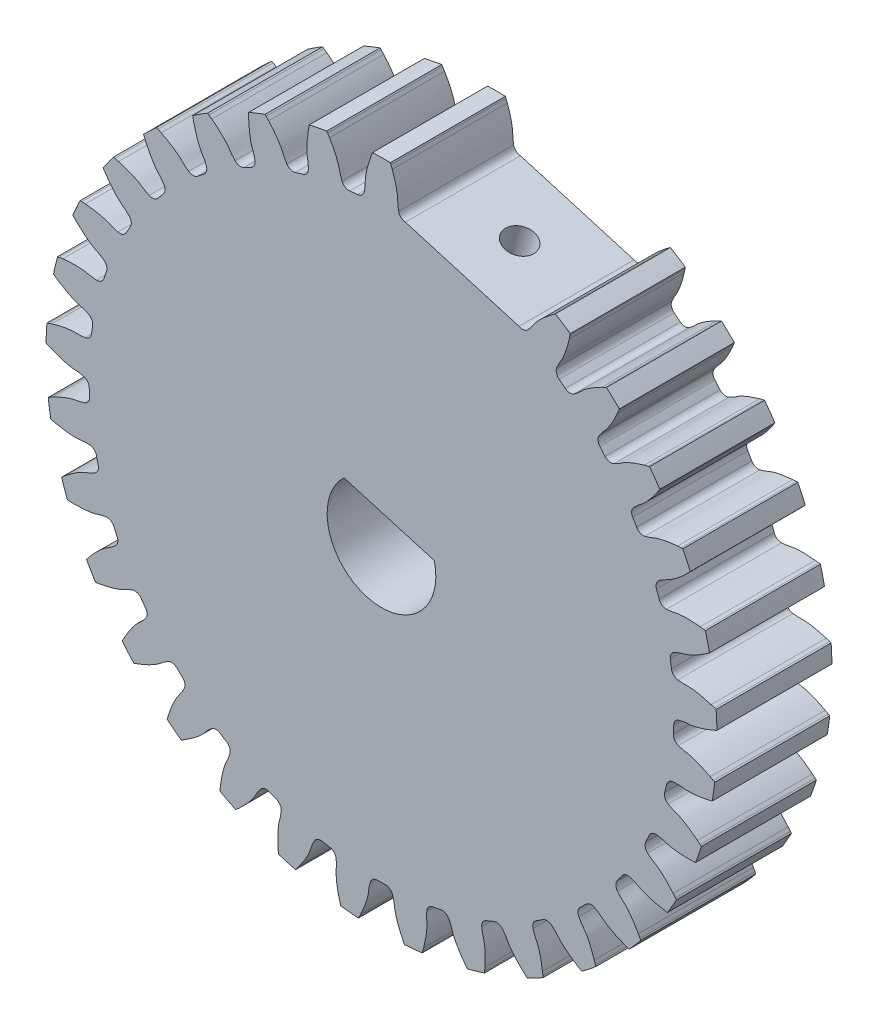
SolidWorks part; units mm, degrees
ref_plane "Front Plane" through (0, 0, 0) normal (0, 0, 1) x (1, 0, 0)
ref_plane "Top Plane" through (0, 0, 0) normal (0, 1, 0) x (1, 0, 0)
ref_plane "Right Plane" through (0, 0, 0) normal (1, 0, 0) x (0, 0, -1)
sketch "Sketch1" plane through (0, 0, 0) normal (0, 0, 1) x (1, 0, 0)
  line L0 (1.3177, 16.0878) -> (7.5892, 14.2464)
  line L1 (-2.0702, 2.1712) -> (2.9154, 0.7073)
  arc A0 (-2.0702, 2.1712) -> (2.9154, 0.7073) centre (0, 0) ccw
  arc A2 (0.9461, 16.421) -> (1.3177, 16.0878) centre (1.3514, 16.4992) ccw
  arc A4 (7.5892, 14.2464) -> (8.0819, 14.3257) centre (7.7833, 14.6106) ccw
  arc A5 (9.6738, 13.3027) -> (9.8063, 12.8215) centre (10.057, 13.1494) ccw
  arc A6 (10.1482, 12.5526) -> (9.8063, 12.8215) centre (0, 0) ccw
  arc A7 (10.1482, 12.5526) -> (10.647, 12.5373) centre (10.4077, 12.8736) ccw
  arc A8 (12.0165, 11.2315) -> (12.0556, 10.734) centre (12.3638, 11.0084) ccw
  arc A9 (12.3404, 10.4052) -> (12.0556, 10.734) centre (0, 0) ccw
  arc A10 (12.3404, 10.4052) -> (12.8273, 10.2958) centre (12.6559, 10.6713) ccw
  arc A11 (13.925, 8.7544) -> (13.8691, 8.2585) centre (14.2237, 8.4696) ccw
  arc A12 (14.0866, 7.8818) -> (13.8691, 8.2585) centre (0, 0) ccw
  arc A13 (14.0866, 7.8818) -> (14.544, 7.6822) centre (14.4468, 8.0833) ccw
  arc A14 (15.3301, 5.9609) -> (15.1814, 5.4845) centre (15.5696, 5.6247) ccw
  arc A15 (15.3237, 5.0734) -> (15.1814, 5.4845) centre (0, 0) ccw
  arc A16 (15.3237, 5.0734) -> (15.735, 4.7909) centre (15.7155, 5.2032) ccw
  arc A17 (16.1812, 2.9519) -> (15.945, 2.5123) centre (16.3527, 2.5765) ccw
  arc A18 (16.0069, 2.0817) -> (15.945, 2.5123) centre (0, 0) ccw
  arc A19 (16.0069, 2.0817) -> (16.3574, 1.7264) centre (16.4162, 2.135) ccw
  arc A20 (16.4474, -0.1637) -> (16.1323, -0.5507) centre (16.5448, -0.5648) ccw
  arc A21 (16.1116, -0.9852) -> (16.1323, -0.5507) centre (0, 0) ccw
  arc A22 (16.1116, -0.9852) -> (16.3885, -1.4004) centre (16.5236, -1.0104) ccw
  arc A23 (16.1192, -3.2735) -> (15.7365, -3.5938) centre (16.1389, -3.6857) ccw
  arc A24 (15.634, -4.0166) -> (15.7365, -3.5938) centre (0, 0) ccw
  arc A25 (15.634, -4.0166) -> (15.8273, -4.4767) centre (16.0338, -4.1193) ccw
  arc A26 (15.2084, -6.2649) -> (14.772, -6.5071) centre (15.1497, -6.6734) ccw
  arc A27 (14.5913, -6.9027) -> (14.772, -6.5071) centre (0, 0) ccw
  arc A28 (14.5913, -6.9027) -> (14.6941, -7.3911) centre (14.9644, -7.0792) ccw
  arc A29 (13.7479, -9.0299) -> (13.2736, -9.1851) centre (13.613, -9.42) ccw
  arc A30 (13.0213, -9.5394) -> (13.2736, -9.1851) centre (0, 0) ccw
  arc A31 (13.0213, -9.5394) -> (13.0297, -10.0384) centre (13.3543, -9.7833) ccw
  arc A32 (11.7906, -11.4685) -> (11.2954, -11.5312) centre (11.5843, -11.826) ccw
  arc A33 (10.9806, -11.8313) -> (11.2954, -11.5312) centre (0, 0) ccw
  arc A34 (10.9806, -11.8313) -> (10.8945, -12.3229) centre (11.2614, -12.1339) ccw
  arc A35 (9.4071, -13.4926) -> (8.909, -13.4604) centre (9.1368, -13.8046) ccw
  arc A36 (8.5431, -13.6956) -> (8.909, -13.4604) centre (0, 0) ccw
  arc A37 (8.5431, -13.6956) -> (8.3655, -14.162) centre (8.7616, -14.0458) ccw
  arc A38 (6.6836, -15.0291) -> (6.2006, -14.9032) centre (6.3592, -15.2843) ccw
  arc A39 (5.7968, -15.0649) -> (6.2006, -14.9032) centre (0, 0) ccw
  arc A40 (5.7968, -15.0649) -> (5.5341, -15.4893) centre (5.945, -15.4501) ccw
  arc A41 (3.7185, -16.0224) -> (3.2681, -15.8074) centre (3.3517, -16.2116) ccw
  arc A42 (2.841, -15.8897) -> (3.2681, -15.8074) centre (0, 0) ccw
  arc A43 (2.841, -15.8897) -> (2.5028, -16.2567) centre (2.9136, -16.296) ccw
  arc A44 (0.6191, -16.4366) -> (0.2175, -16.1402) centre (0.2231, -16.5529) ccw
  arc A45 (-0.2175, -16.1402) -> (0.2175, -16.1402) centre (0, 0) ccw
  arc A46 (-0.2175, -16.1402) -> (-0.6191, -16.4366) centre (-0.2231, -16.5529) ccw
  arc A47 (-2.5028, -16.2567) -> (-2.841, -15.8897) centre (-2.9136, -16.296) ccw
  arc A48 (-3.2681, -15.8074) -> (-2.841, -15.8897) centre (0, 0) ccw
  arc A49 (-3.2681, -15.8074) -> (-3.7185, -16.0224) centre (-3.3517, -16.2116) ccw
  arc A50 (-5.5341, -15.4893) -> (-5.7968, -15.0649) centre (-5.945, -15.4501) ccw
  arc A51 (-6.2006, -14.9032) -> (-5.7968, -15.0649) centre (0, 0) ccw
  arc A52 (-6.2006, -14.9032) -> (-6.6836, -15.0291) centre (-6.3592, -15.2843) ccw
  arc A53 (-8.3655, -14.162) -> (-8.5431, -13.6956) centre (-8.7616, -14.0458) ccw
  arc A54 (-8.909, -13.4604) -> (-8.5431, -13.6956) centre (0, 0) ccw
  arc A55 (-8.909, -13.4604) -> (-9.4071, -13.4926) centre (-9.1368, -13.8046) ccw
  arc A56 (-10.8945, -12.3229) -> (-10.9806, -11.8313) centre (-11.2614, -12.1339) ccw
  arc A57 (-11.2954, -11.5312) -> (-10.9806, -11.8313) centre (0, 0) ccw
  arc A58 (-11.2954, -11.5312) -> (-11.7906, -11.4685) centre (-11.5843, -11.826) ccw
  arc A59 (-13.0297, -10.0384) -> (-13.0213, -9.5394) centre (-13.3543, -9.7833) ccw
  arc A60 (-13.2736, -9.1851) -> (-13.0213, -9.5394) centre (0, 0) ccw
  arc A61 (-13.2736, -9.1851) -> (-13.7479, -9.0299) centre (-13.613, -9.42) ccw
  arc A62 (-14.6941, -7.3911) -> (-14.5913, -6.9027) centre (-14.9644, -7.0792) ccw
  arc A63 (-14.772, -6.5071) -> (-14.5913, -6.9027) centre (0, 0) ccw
  arc A64 (-14.772, -6.5071) -> (-15.2084, -6.2649) centre (-15.1497, -6.6734) ccw
  arc A65 (-15.8273, -4.4767) -> (-15.634, -4.0166) centre (-16.0338, -4.1193) ccw
  arc A66 (-15.7365, -3.5938) -> (-15.634, -4.0166) centre (0, 0) ccw
  arc A67 (-15.7365, -3.5938) -> (-16.1192, -3.2735) centre (-16.1389, -3.6857) ccw
  arc A68 (-16.3885, -1.4004) -> (-16.1116, -0.9852) centre (-16.5236, -1.0104) ccw
  arc A69 (-16.1323, -0.5507) -> (-16.1116, -0.9852) centre (0, 0) ccw
  arc A70 (-16.1323, -0.5507) -> (-16.4474, -0.1637) centre (-16.5448, -0.5648) ccw
  arc A71 (-16.3574, 1.7264) -> (-16.0069, 2.0817) centre (-16.4162, 2.135) ccw
  arc A72 (-15.945, 2.5123) -> (-16.0069, 2.0817) centre (0, 0) ccw
  arc A73 (-15.945, 2.5123) -> (-16.1812, 2.9519) centre (-16.3527, 2.5765) ccw
  arc A74 (-15.735, 4.7909) -> (-15.3237, 5.0734) centre (-15.7155, 5.2032) ccw
  arc A75 (-15.1814, 5.4845) -> (-15.3237, 5.0734) centre (0, 0) ccw
  arc A76 (-15.1814, 5.4845) -> (-15.3301, 5.9609) centre (-15.5696, 5.6247) ccw
  arc A77 (-14.544, 7.6822) -> (-14.0866, 7.8818) centre (-14.4468, 8.0833) ccw
  arc A78 (-13.8691, 8.2585) -> (-14.0866, 7.8818) centre (0, 0) ccw
  arc A79 (-13.8691, 8.2585) -> (-13.925, 8.7544) centre (-14.2237, 8.4696) ccw
  arc A80 (-12.8273, 10.2958) -> (-12.3404, 10.4052) centre (-12.6559, 10.6713) ccw
  arc A81 (-12.0556, 10.734) -> (-12.3404, 10.4052) centre (0, 0) ccw
  arc A82 (-12.0556, 10.734) -> (-12.0165, 11.2315) centre (-12.3638, 11.0084) ccw
  arc A83 (-10.647, 12.5373) -> (-10.1482, 12.5526) centre (-10.4077, 12.8736) ccw
  arc A84 (-9.8063, 12.8215) -> (-10.1482, 12.5526) centre (0, 0) ccw
  arc A85 (-9.8063, 12.8215) -> (-9.6738, 13.3027) centre (-10.057, 13.1494) ccw
  arc A86 (-8.0819, 14.3257) -> (-7.5892, 14.2464) centre (-7.7833, 14.6106) ccw
  arc A87 (-7.2026, 14.4457) -> (-7.5892, 14.2464) centre (0, 0) ccw
  arc A88 (-7.2026, 14.4457) -> (-6.9814, 14.8931) centre (-7.3867, 14.8151) ccw
  arc A89 (-5.2247, 15.5964) -> (-4.7559, 15.4252) centre (-4.8775, 15.8196) ccw
  arc A90 (-4.3386, 15.5477) -> (-4.7559, 15.4252) centre (0, 0) ccw
  arc A91 (-4.3386, 15.5477) -> (-4.0367, 15.9452) centre (-4.4495, 15.9453) ccw
  arc A92 (-2.1786, 16.3033) -> (-1.7507, 16.0465) centre (-1.7955, 16.4568) ccw
  arc A93 (-1.3177, 16.0878) -> (-1.7507, 16.0465) centre (0, 0) ccw
  arc A94 (-1.3177, 16.0878) -> (-0.9461, 16.421) centre (-1.3514, 16.4992) ccw
  arc A95 (10.4216, 15.3105) -> (9.5977, 15.84) centre (0, 0) ccw
  arc A96 (-14.3129, -11.7542) -> (-13.6715, -12.4944) centre (0, 0) ccw
  arc A97 (-16.6378, 8.1366) -> (-17.0447, 7.2457) centre (0, 0) ccw
  arc A98 (17.0447, 7.2457) -> (16.6378, 8.1366) centre (0, 0) ccw
  arc A99 (11.0599, -14.856) -> (11.8297, -14.2506) centre (0, 0) ccw
  arc A100 (-18.3956, -2.1502) -> (-18.2562, -3.1196) centre (0, 0) ccw
  arc A101 (17.3359, -6.5182) -> (17.6562, -5.5927) centre (0, 0) ccw
  arc A102 (4.7462, -17.9024) -> (5.6859, -17.6264) centre (0, 0) ccw
  arc A103 (18.1079, 3.889) -> (17.877, 4.8408) centre (0, 0) ccw
  arc A104 (-12.422, 13.7374) -> (-13.1308, 13.0615) centre (0, 0) ccw
  arc A105 (-17.877, 4.8408) -> (-18.1079, 3.889) centre (0, 0) ccw
  arc A106 (-9.5977, 15.84) -> (-10.4216, 15.3105) centre (0, 0) ccw
  arc A107 (-5.6859, -17.6264) -> (-4.7462, -17.9024) centre (0, 0) ccw
  arc A108 (0.4897, 18.5144) -> (-0.4897, 18.5144) centre (0, 0) ccw
  arc A109 (-11.8297, -14.2506) -> (-11.0599, -14.856) centre (0, 0) ccw
  arc A110 (-16.2787, -8.8331) -> (-15.7891, -9.6813) centre (0, 0) ccw
  arc A111 (1.2724, -18.4771) -> (2.2474, -18.384) centre (0, 0) ccw
  arc A112 (-3.023, 18.2725) -> (-3.9847, 18.0871) centre (0, 0) ccw
  arc A113 (18.5167, 0.3918) -> (18.4701, 1.3701) centre (0, 0) ccw
  arc A114 (13.1308, 13.0615) -> (12.422, 13.7374) centre (0, 0) ccw
  arc A115 (8.0485, -16.6806) -> (8.919, -16.2318) centre (0, 0) ccw
  arc A116 (13.6715, -12.4944) -> (14.3129, -11.7542) centre (0, 0) ccw
  arc A117 (-18.4701, 1.3701) -> (-18.5167, 0.3918) centre (0, 0) ccw
  arc A118 (-2.2474, -18.384) -> (-1.2724, -18.4771) centre (0, 0) ccw
  arc A119 (15.3654, 10.3405) -> (14.7973, 11.1383) centre (0, 0) ccw
  arc A120 (-8.919, -16.2318) -> (-8.0485, -16.6806) centre (0, 0) ccw
  arc A121 (15.7891, -9.6813) -> (16.2787, -8.8331) centre (0, 0) ccw
  arc A122 (-14.7973, 11.1383) -> (-15.3654, 10.3405) centre (0, 0) ccw
  arc A123 (-17.6562, -5.5927) -> (-17.3359, -6.5182) centre (0, 0) ccw
  arc A124 (18.2562, -3.1196) -> (18.3956, -2.1502) centre (0, 0) ccw
  arc A125 (-6.4265, 17.3701) -> (-7.3357, 17.0061) centre (0, 0) ccw
  spline S31 degree 3 poles (-11.7906, -11.4685) (-11.8581, -11.5075) (-11.9247, -11.5479) (-12.0526, -11.6363) (-12.1128, -11.6859) (-12.2326, -11.7859) (-12.2929, -11.8353) (-12.421, -11.9234) (-12.4877, -11.9637) (-12.8258, -12.1584) (-13.1079, -12.2893) (-13.4001, -12.3987) knots 0 0 0 0 0.125 0.125 0.25 0.25 0.375 0.375 0.5 0.5 1 1 1 1
  spline S32 degree 3 poles (-6.6836, -15.0291) (-6.7318, -15.0904) (-6.7786, -15.1527) (-6.8644, -15.2823) (-6.9019, -15.3507) (-6.9759, -15.4881) (-7.0136, -15.5563) (-7.0998, -15.6857) (-7.1467, -15.7479) (-7.3882, -16.0543) (-7.6014, -16.2807) (-7.8321, -16.4909) knots 0 0 0 0 0.125 0.125 0.25 0.25 0.375 0.375 0.5 0.5 1 1 1 1
  spline S33 degree 3 poles (-3.7185, -16.0224) (-3.7543, -16.0917) (-3.7885, -16.1617) (-3.8482, -16.3052) (-3.872, -16.3795) (-3.9187, -16.5284) (-3.9428, -16.6025) (-4.0029, -16.7459) (-4.0372, -16.8158) (-4.2164, -17.1624) (-4.3829, -17.4251) (-4.5696, -17.6751) knots 0 0 0 0 0.125 0.125 0.25 0.25 0.375 0.375 0.5 0.5 1 1 1 1
  spline S34 degree 3 poles (-16.1812, 2.9519) (-16.2521, 2.9843) (-16.3237, 3.0152) (-16.4699, 3.068) (-16.5452, 3.0883) (-16.6961, 3.1278) (-16.7713, 3.1484) (-16.9174, 3.2016) (-16.9889, 3.2325) (-17.3436, 3.395) (-17.6139, 3.5488) (-17.8725, 3.7234) knots 0 0 0 0 0.125 0.125 0.25 0.25 0.375 0.375 0.5 0.5 1 1 1 1
  spline S35 degree 3 poles (-4.0367, 15.9452) (-4.0367, 16.0232) (-4.0384, 16.1011) (-4.0511, 16.256) (-4.0639, 16.3329) (-4.0906, 16.4867) (-4.1032, 16.5636) (-4.1155, 16.7186) (-4.117, 16.7965) (-4.1166, 17.1866) (-4.0889, 17.4964) (-4.0376, 17.8042) knots 0 0 0 0 0.125 0.125 0.25 0.25 0.375 0.375 0.5 0.5 1 1 1 1
  spline S36 degree 3 poles (-16.1192, -3.2735) (-16.1971, -3.2697) (-16.275, -3.2677) (-16.4304, -3.273) (-16.5078, -3.2821) (-16.6626, -3.3015) (-16.7401, -3.3104) (-16.8955, -3.3153) (-16.9733, -3.3132) (-17.363, -3.2941) (-17.6712, -3.2518) (-17.9761, -3.1858) knots 0 0 0 0 0.125 0.125 0.25 0.25 0.375 0.375 0.5 0.5 1 1 1 1
  spline S37 degree 3 poles (-16.4474, -0.1637) (-16.5232, -0.1453) (-16.5993, -0.1286) (-16.7529, -0.1044) (-16.8306, -0.0987) (-16.9863, -0.0884) (-17.0641, -0.0825) (-17.2176, -0.0579) (-17.2936, -0.0411) (-17.6727, 0.0514) (-17.9672, 0.1513) (-18.2542, 0.2737) knots 0 0 0 0 0.125 0.125 0.25 0.25 0.375 0.375 0.5 0.5 1 1 1 1
  spline S38 degree 3 poles (-15.3301, 5.9609) (-15.3936, 6.0062) (-15.4581, 6.0499) (-15.5916, 6.1295) (-15.6617, 6.1637) (-15.8024, 6.2311) (-15.8724, 6.2655) (-16.0058, 6.3454) (-16.0701, 6.3893) (-16.3876, 6.616) (-16.624, 6.8182) (-16.8449, 7.0385) knots 0 0 0 0 0.125 0.125 0.25 0.25 0.375 0.375 0.5 0.5 1 1 1 1
  spline S39 degree 3 poles (5.5341, -15.4893) (5.5415, -15.5669) (5.5506, -15.6443) (5.578, -15.7973) (5.598, -15.8727) (5.6393, -16.0232) (5.6591, -16.0986) (5.686, -16.2517) (5.695, -16.3291) (5.7316, -16.7175) (5.7336, -17.0285) (5.7117, -17.3398) knots 0 0 0 0 0.125 0.125 0.25 0.25 0.375 0.375 0.5 0.5 1 1 1 1
  spline S40 degree 3 poles (14.6941, -7.3911) (14.753, -7.4422) (14.813, -7.4919) (14.9384, -7.5838) (15.0049, -7.6245) (15.1386, -7.705) (15.205, -7.7459) (15.3301, -7.8381) (15.39, -7.8879) (15.6846, -8.1438) (15.9006, -8.3675) (16.0995, -8.6079) knots 0 0 0 0 0.125 0.125 0.25 0.25 0.375 0.375 0.5 0.5 1 1 1 1
  spline S41 degree 3 poles (2.5028, -16.2567) (2.4953, -16.3344) (2.4896, -16.412) (2.4875, -16.5675) (2.493, -16.6453) (2.505, -16.8009) (2.5102, -16.8786) (2.5076, -17.0341) (2.5018, -17.1118) (2.4642, -17.5001) (2.4073, -17.8059) (2.3269, -18.1074) knots 0 0 0 0 0.125 0.125 0.25 0.25 0.375 0.375 0.5 0.5 1 1 1 1
  spline S42 degree 3 poles (12.8273, 10.2958) (12.8983, 10.3282) (12.9684, 10.3621) (13.1041, 10.438) (13.1688, 10.4816) (13.2975, 10.5698) (13.3623, 10.6132) (13.4981, 10.6887) (13.5683, 10.7225) (13.9234, 10.8841) (14.2167, 10.9877) (14.518, 11.0688) knots 0 0 0 0 0.125 0.125 0.25 0.25 0.375 0.375 0.5 0.5 1 1 1 1
  spline S43 degree 3 poles (8.3655, -14.162) (8.3875, -14.2369) (8.411, -14.3111) (8.4668, -14.4562) (8.5008, -14.5264) (8.5698, -14.6664) (8.6035, -14.7367) (8.6589, -14.8819) (8.6824, -14.9562) (8.7918, -15.3307) (8.8526, -15.6357) (8.89, -15.9455) knots 0 0 0 0 0.125 0.125 0.25 0.25 0.375 0.375 0.5 0.5 1 1 1 1
  spline S44 degree 3 poles (-13.925, 8.7544) (-13.9788, 8.8109) (-14.0338, 8.8661) (-14.1498, 8.9695) (-14.2122, 9.0163) (-14.3376, 9.1091) (-14.3998, 9.1561) (-14.5157, 9.2598) (-14.5705, 9.3151) (-14.8394, 9.5978) (-15.0332, 9.8411) (-15.2084, 10.0992) knots 0 0 0 0 0.125 0.125 0.25 0.25 0.375 0.375 0.5 0.5 1 1 1 1
  spline S45 degree 3 poles (10.647, 12.5373) (10.7106, 12.5826) (10.773, 12.6291) (10.8919, 12.7293) (10.9471, 12.7844) (11.0568, 12.8953) (11.1122, 12.9502) (11.2314, 13.0501) (11.2939, 13.0966) (11.612, 13.3225) (11.8803, 13.4797) (12.1608, 13.6163) knots 0 0 0 0 0.125 0.125 0.25 0.25 0.375 0.375 0.5 0.5 1 1 1 1
  spline S46 degree 3 poles (-0.6191, -16.4366) (-0.6411, -16.5114) (-0.6614, -16.5866) (-0.6929, -16.7389) (-0.7022, -16.8163) (-0.7199, -16.9713) (-0.7295, -17.0487) (-0.7614, -17.2008) (-0.7818, -17.276) (-0.8922, -17.6502) (-1.006, -17.9397) (-1.142, -18.2205) knots 0 0 0 0 0.125 0.125 0.25 0.25 0.375 0.375 0.5 0.5 1 1 1 1
  spline S47 degree 3 poles (15.735, 4.7909) (15.813, 4.7946) (15.8907, 4.8) (16.0449, 4.82) (16.1211, 4.8365) (16.2734, 4.8705) (16.3496, 4.8867) (16.5038, 4.9063) (16.5816, 4.9116) (16.9713, 4.9297) (17.282, 4.9168) (17.5919, 4.8802) knots 0 0 0 0 0.125 0.125 0.25 0.25 0.375 0.375 0.5 0.5 1 1 1 1
  spline S48 degree 3 poles (-6.9814, 14.8931) (-6.9962, 14.9697) (-7.0126, 15.0458) (-7.0543, 15.1956) (-7.0815, 15.2687) (-7.1368, 15.4146) (-7.1637, 15.4877) (-7.2051, 15.6376) (-7.2214, 15.7138) (-7.2948, 16.097) (-7.3263, 16.4064) (-7.3341, 16.7183) knots 0 0 0 0 0.125 0.125 0.25 0.25 0.375 0.375 0.5 0.5 1 1 1 1
  spline S49 degree 3 poles (-13.7479, -9.0299) (-13.8217, -9.0554) (-13.8947, -9.0825) (-14.037, -9.1451) (-14.1055, -9.1824) (-14.242, -9.2579) (-14.3106, -9.295) (-14.453, -9.3572) (-14.5261, -9.3842) (-14.895, -9.5113) (-15.1968, -9.5866) (-15.5044, -9.6387) knots 0 0 0 0 0.125 0.125 0.25 0.25 0.375 0.375 0.5 0.5 1 1 1 1
  spline S50 degree 3 poles (16.3885, -1.4004) (16.4622, -1.426) (16.5364, -1.4498) (16.6869, -1.4886) (16.7638, -1.5016) (16.9178, -1.5266) (16.9947, -1.5399) (17.1451, -1.579) (17.2192, -1.603) (17.5878, -1.731) (17.8715, -1.8585) (18.1455, -2.0077) knots 0 0 0 0 0.125 0.125 0.25 0.25 0.375 0.375 0.5 0.5 1 1 1 1
  spline S51 degree 3 poles (14.544, 7.6822) (14.6198, 7.7005) (14.6951, 7.7206) (14.8427, 7.7694) (14.9144, 7.8) (15.0575, 7.8622) (15.1293, 7.8926) (15.2771, 7.941) (15.3524, 7.9609) (15.7316, 8.0524) (16.0392, 8.0986) (16.3504, 8.1213) knots 0 0 0 0 0.125 0.125 0.25 0.25 0.375 0.375 0.5 0.5 1 1 1 1
  spline S52 degree 3 poles (16.3574, 1.7264) (16.4346, 1.7153) (16.5119, 1.7059) (16.6671, 1.6964) (16.745, 1.6981) (16.901, 1.7027) (16.979, 1.7042) (17.1341, 1.6943) (17.2114, 1.6847) (17.5975, 1.6288) (17.9002, 1.5573) (18.1976, 1.4627) knots 0 0 0 0 0.125 0.125 0.25 0.25 0.375 0.375 0.5 0.5 1 1 1 1
  spline S53 degree 3 poles (-9.4071, -13.4926) (-9.466, -13.5437) (-9.5238, -13.596) (-9.6326, -13.707) (-9.6823, -13.7671) (-9.781, -13.888) (-9.8309, -13.9479) (-9.94, -14.0586) (-9.9978, -14.1108) (-10.293, -14.3659) (-10.5452, -14.5479) (-10.8114, -14.7107) knots 0 0 0 0 0.125 0.125 0.25 0.25 0.375 0.375 0.5 0.5 1 1 1 1
  spline S54 degree 3 poles (-9.6738, 13.3027) (-9.7028, 13.3751) (-9.7333, 13.4468) (-9.8026, 13.5859) (-9.8431, 13.6526) (-9.9251, 13.7854) (-9.9654, 13.8521) (-10.0343, 13.9914) (-10.0647, 14.0632) (-10.2093, 14.4255) (-10.2988, 14.7234) (-10.3655, 15.0282) knots 0 0 0 0 0.125 0.125 0.25 0.25 0.375 0.375 0.5 0.5 1 1 1 1
  spline S55 degree 3 poles (13.0297, -10.0384) (13.078, -10.0998) (13.1274, -10.1599) (13.2332, -10.2739) (13.2908, -10.3264) (13.4068, -10.4307) (13.4643, -10.4834) (13.5697, -10.5977) (13.6191, -10.6579) (13.8599, -10.9649) (14.0297, -11.2255) (14.1796, -11.4992) knots 0 0 0 0 0.125 0.125 0.25 0.25 0.375 0.375 0.5 0.5 1 1 1 1
  spline S56 degree 3 poles (-12.0165, 11.2315) (-12.0587, 11.2972) (-12.1022, 11.3618) (-12.1967, 11.4853) (-12.249, 11.543) (-12.3546, 11.6579) (-12.4068, 11.7158) (-12.5009, 11.8396) (-12.5443, 11.9043) (-12.7549, 12.2327) (-12.8991, 12.5083) (-13.0223, 12.7949) knots 0 0 0 0 0.125 0.125 0.25 0.25 0.375 0.375 0.5 0.5 1 1 1 1
  spline S57 degree 3 poles (-15.2084, -6.2649) (-15.2856, -6.276) (-15.3625, -6.2887) (-15.514, -6.3233) (-15.5883, -6.347) (-15.7367, -6.3953) (-15.8111, -6.4187) (-15.9627, -6.4529) (-16.0396, -6.4655) (-16.4258, -6.5206) (-16.7364, -6.5373) (-17.0483, -6.5303) knots 0 0 0 0 0.125 0.125 0.25 0.25 0.375 0.375 0.5 0.5 1 1 1 1
  spline S58 degree 3 poles (15.8273, -4.4767) (15.8949, -4.5157) (15.9631, -4.5532) (16.1037, -4.6197) (16.1767, -4.647) (16.3232, -4.7007) (16.3961, -4.7283) (16.5365, -4.7952) (16.6047, -4.8328) (16.9423, -5.0283) (17.1968, -5.2071) (17.4377, -5.4054) knots 0 0 0 0 0.125 0.125 0.25 0.25 0.375 0.375 0.5 0.5 1 1 1 1
  spline S59 degree 3 poles (10.8945, -12.3229) (10.9302, -12.3923) (10.9674, -12.4607) (11.0497, -12.5926) (11.0963, -12.6551) (11.1905, -12.7795) (11.237, -12.8421) (11.3189, -12.9743) (11.356, -13.0428) (11.5343, -13.3898) (11.6517, -13.6778) (11.7471, -13.9749) knots 0 0 0 0 0.125 0.125 0.25 0.25 0.375 0.375 0.5 0.5 1 1 1 1
  spline S60 degree 3 poles (8.0819, 14.3257) (8.1358, 14.3822) (8.1883, 14.4397) (8.286, 14.5606) (8.3298, 14.6251) (8.4166, 14.7548) (8.4606, 14.8192) (8.5586, 14.9398) (8.6113, 14.9973) (8.8808, 15.2793) (9.1146, 15.4844) (9.3642, 15.6717) knots 0 0 0 0 0.125 0.125 0.25 0.25 0.375 0.375 0.5 0.5 1 1 1 1
  spline S61 degree 3 poles (-6.229, 17.1607) (-6.0194, 16.9296) (-5.8286, 16.6837) (-5.6173, 16.3559) (-5.5766, 16.2895) (-5.5031, 16.1525) (-5.4721, 16.081) (-5.4115, 15.9372) (-5.3807, 15.8656) (-5.3076, 15.7284) (-5.2669, 15.662) (-5.2247, 15.5964) knots 0 0 0 0 0.5 0.5 0.625 0.625 0.75 0.75 0.875 0.875 1 1 1 1
  spline S62 degree 3 poles (-9.3642, 15.6717) (-9.1146, 15.4844) (-8.8807, 15.2792) (-8.6112, 14.9972) (-8.5586, 14.9398) (-8.4605, 14.8191) (-8.4165, 14.7548) (-8.3298, 14.6251) (-8.286, 14.5606) (-8.1883, 14.4397) (-8.1358, 14.3822) (-8.0819, 14.3257) knots 0 0 0 0 0.5 0.5 0.625 0.625 0.75 0.75 0.875 0.875 1 1 1 1
  spline S63 degree 3 poles (-11.7471, -13.9749) (-11.6517, -13.6778) (-11.5342, -13.3896) (-11.3559, -13.0427) (-11.3188, -12.9742) (-11.2369, -12.8421) (-11.1905, -12.7795) (-11.0963, -12.6551) (-11.0497, -12.5926) (-10.9674, -12.4607) (-10.9302, -12.3922) (-10.8945, -12.3229) knots 0 0 0 0 0.5 0.5 0.625 0.625 0.75 0.75 0.875 0.875 1 1 1 1
  spline S64 degree 3 poles (-8.89, -15.9455) (-8.8526, -15.6357) (-8.7918, -15.3305) (-8.6824, -14.9561) (-8.6589, -14.8818) (-8.6035, -14.7366) (-8.5697, -14.6663) (-8.5008, -14.5264) (-8.4668, -14.4562) (-8.411, -14.3111) (-8.3875, -14.2369) (-8.3655, -14.162) knots 0 0 0 0 0.5 0.5 0.625 0.625 0.75 0.75 0.875 0.875 1 1 1 1
  spline S65 degree 3 poles (-16.0995, -8.6079) (-15.9006, -8.3675) (-15.6844, -8.1436) (-15.39, -7.8878) (-15.3301, -7.838) (-15.2049, -7.7458) (-15.1385, -7.705) (-15.0049, -7.6245) (-14.9383, -7.5838) (-14.813, -7.4919) (-14.753, -7.4422) (-14.6941, -7.3911) knots 0 0 0 0 0.5 0.5 0.625 0.625 0.75 0.75 0.875 0.875 1 1 1 1
  spline S66 degree 3 poles (16.8449, 7.0385) (16.624, 6.8182) (16.3875, 6.6159) (16.0701, 6.3892) (16.0057, 6.3453) (15.8724, 6.2654) (15.8024, 6.2311) (15.6617, 6.1637) (15.5916, 6.1295) (15.458, 6.0499) (15.3936, 6.0061) (15.3301, 5.9609) knots 0 0 0 0 0.5 0.5 0.625 0.625 0.75 0.75 0.875 0.875 1 1 1 1
  spline S67 degree 3 poles (-14.518, 11.0688) (-14.2167, 10.9877) (-13.9233, 10.8841) (-13.5683, 10.7225) (-13.4981, 10.6887) (-13.3622, 10.6132) (-13.2975, 10.5698) (-13.1687, 10.4816) (-13.1041, 10.438) (-12.9684, 10.3621) (-12.8983, 10.3282) (-12.8273, 10.2958) knots 0 0 0 0 0.5 0.5 0.625 0.625 0.75 0.75 0.875 0.875 1 1 1 1
  spline S68 degree 3 poles (-5.7117, -17.3398) (-5.7336, -17.0285) (-5.7316, -16.7173) (-5.695, -16.329) (-5.686, -16.2516) (-5.6591, -16.0985) (-5.6393, -16.0231) (-5.598, -15.8726) (-5.578, -15.7973) (-5.5506, -15.6443) (-5.5415, -15.5669) (-5.5341, -15.4893) knots 0 0 0 0 0.5 0.5 0.625 0.625 0.75 0.75 0.875 0.875 1 1 1 1
  spline S69 degree 3 poles (-14.1796, -11.4992) (-14.0297, -11.2255) (-13.8598, -10.9648) (-13.6191, -10.6579) (-13.5697, -10.5976) (-13.4642, -10.4834) (-13.4068, -10.4307) (-13.2908, -10.3264) (-13.2331, -10.2739) (-13.1274, -10.1599) (-13.078, -10.0997) (-13.0297, -10.0384) knots 0 0 0 0 0.5 0.5 0.625 0.625 0.75 0.75 0.875 0.875 1 1 1 1
  spline S70 degree 3 poles (-17.5919, 4.8802) (-17.282, 4.9168) (-16.9711, 4.9297) (-16.5815, 4.9116) (-16.5038, 4.9063) (-16.3496, 4.8867) (-16.2733, 4.8705) (-16.121, 4.8364) (-16.0448, 4.82) (-15.8907, 4.8) (-15.813, 4.7946) (-15.735, 4.7909) knots 0 0 0 0 0.5 0.5 0.625 0.625 0.75 0.75 0.875 0.875 1 1 1 1
  spline S71 degree 3 poles (7.8321, -16.4909) (7.6014, -16.2807) (7.3881, -16.0542) (7.1466, -15.7478) (7.0997, -15.6857) (7.0136, -15.5563) (6.9759, -15.488) (6.9019, -15.3507) (6.8644, -15.2823) (6.7786, -15.1527) (6.7318, -15.0904) (6.6836, -15.0291) knots 0 0 0 0 0.5 0.5 0.625 0.625 0.75 0.75 0.875 0.875 1 1 1 1
  spline S72 degree 3 poles (-16.3504, 8.1213) (-16.0392, 8.0986) (-15.7315, 8.0524) (-15.3523, 7.9609) (-15.277, 7.941) (-15.1293, 7.8925) (-15.0575, 7.8622) (-14.9144, 7.8) (-14.8427, 7.7694) (-14.6951, 7.7205) (-14.6198, 7.7005) (-14.544, 7.6822) knots 0 0 0 0 0.5 0.5 0.625 0.625 0.75 0.75 0.875 0.875 1 1 1 1
  spline S73 degree 3 poles (10.8114, -14.7107) (10.5452, -14.5479) (10.2929, -14.3658) (9.9978, -14.1107) (9.94, -14.0586) (9.8309, -13.9478) (9.781, -13.8879) (9.6823, -13.7671) (9.6326, -13.707) (9.5238, -13.596) (9.466, -13.5437) (9.4071, -13.4926) knots 0 0 0 0 0.5 0.5 0.625 0.625 0.75 0.75 0.875 0.875 1 1 1 1
  spline S74 degree 3 poles (-17.4377, -5.4054) (-17.1968, -5.2071) (-16.9422, -5.0282) (-16.6046, -4.8327) (-16.5364, -4.7952) (-16.3961, -4.7283) (-16.3231, -4.7007) (-16.1766, -4.647) (-16.1036, -4.6197) (-15.9631, -4.5532) (-15.8948, -4.5157) (-15.8273, -4.4767) knots 0 0 0 0 0.5 0.5 0.625 0.625 0.75 0.75 0.875 0.875 1 1 1 1
  spline S75 degree 3 poles (18.2542, 0.2737) (17.9672, 0.1513) (17.6725, 0.0513) (17.2936, -0.0411) (17.2175, -0.0579) (17.064, -0.0825) (16.9863, -0.0885) (16.8306, -0.0987) (16.7528, -0.1044) (16.5993, -0.1286) (16.5232, -0.1453) (16.4474, -0.1637) knots 0 0 0 0 0.5 0.5 0.625 0.625 0.75 0.75 0.875 0.875 1 1 1 1
  spline S76 degree 3 poles (13.0223, 12.7949) (12.8991, 12.5083) (12.7548, 12.2326) (12.5443, 11.9042) (12.5009, 11.8395) (12.4068, 11.7158) (12.3546, 11.6579) (12.249, 11.543) (12.1966, 11.4852) (12.1022, 11.3617) (12.0587, 11.2971) (12.0165, 11.2315) knots 0 0 0 0 0.5 0.5 0.625 0.625 0.75 0.75 0.875 0.875 1 1 1 1
  spline S77 degree 3 poles (-2.3269, -18.1074) (-2.4073, -17.8059) (-2.4643, -17.4999) (-2.5018, -17.1117) (-2.5076, -17.034) (-2.5102, -16.8786) (-2.505, -16.8008) (-2.493, -16.6452) (-2.4875, -16.5674) (-2.4896, -16.412) (-2.4953, -16.3343) (-2.5028, -16.2567) knots 0 0 0 0 0.5 0.5 0.625 0.625 0.75 0.75 0.875 0.875 1 1 1 1
  spline S78 degree 3 poles (17.9761, -3.1858) (17.6711, -3.2518) (17.3629, -3.2941) (16.9733, -3.3132) (16.8954, -3.3153) (16.74, -3.3104) (16.6626, -3.3015) (16.5078, -3.2821) (16.4303, -3.273) (16.275, -3.2677) (16.1971, -3.2697) (16.1192, -3.2735) knots 0 0 0 0 0.5 0.5 0.625 0.625 0.75 0.75 0.875 0.875 1 1 1 1
  spline S79 degree 3 poles (-18.1976, 1.4627) (-17.9002, 1.5573) (-17.5974, 1.6288) (-17.2113, 1.6848) (-17.134, 1.6943) (-16.9789, 1.7042) (-16.901, 1.7027) (-16.745, 1.6981) (-16.667, 1.6964) (-16.5119, 1.7059) (-16.4346, 1.7153) (-16.3574, 1.7264) knots 0 0 0 0 0.5 0.5 0.625 0.625 0.75 0.75 0.875 0.875 1 1 1 1
  spline S80 degree 3 poles (-12.1608, 13.6163) (-11.8803, 13.4797) (-11.6118, 13.3224) (-11.2938, 13.0965) (-11.2313, 13.0501) (-11.1122, 12.9502) (-11.0568, 12.8953) (-10.9471, 12.7844) (-10.8919, 12.7293) (-10.773, 12.6291) (-10.7106, 12.5826) (-10.647, 12.5373) knots 0 0 0 0 0.5 0.5 0.625 0.625 0.75 0.75 0.875 0.875 1 1 1 1
  spline S81 degree 3 poles (1.142, -18.2205) (1.006, -17.9397) (0.8922, -17.65) (0.7818, -17.2759) (0.7614, -17.2008) (0.7295, -17.0486) (0.7199, -16.9713) (0.7022, -16.8162) (0.6929, -16.7388) (0.6614, -16.5866) (0.641, -16.5114) (0.6191, -16.4366) knots 0 0 0 0 0.5 0.5 0.625 0.625 0.75 0.75 0.875 0.875 1 1 1 1
  spline S82 degree 3 poles (-18.1455, -2.0077) (-17.8715, -1.8585) (-17.5876, -1.731) (-17.2192, -1.603) (-17.1451, -1.579) (-16.9946, -1.5399) (-16.9178, -1.5266) (-16.7638, -1.5016) (-16.6869, -1.4885) (-16.5363, -1.4498) (-16.4622, -1.426) (-16.3885, -1.4004) knots 0 0 0 0 0.5 0.5 0.625 0.625 0.75 0.75 0.875 0.875 1 1 1 1
  spline S83 degree 3 poles (15.2084, 10.0992) (15.0332, 9.8411) (14.8393, 9.5977) (14.5705, 9.315) (14.5156, 9.2598) (14.3998, 9.1561) (14.3376, 9.1091) (14.2122, 9.0163) (14.1498, 8.9694) (14.0337, 8.866) (13.9788, 8.8109) (13.925, 8.7544) knots 0 0 0 0 0.5 0.5 0.625 0.625 0.75 0.75 0.875 0.875 1 1 1 1
  spline S84 degree 3 poles (10.3655, 15.0282) (10.2988, 14.7234) (10.2092, 14.4254) (10.0647, 14.0631) (10.0343, 13.9914) (9.9653, 13.8521) (9.9251, 13.7853) (9.8431, 13.6525) (9.8026, 13.5859) (9.7333, 13.4468) (9.7028, 13.3751) (9.6738, 13.3027) knots 0 0 0 0 0.5 0.5 0.625 0.625 0.75 0.75 0.875 0.875 1 1 1 1
  spline S85 degree 3 poles (4.5696, -17.6751) (4.3829, -17.4251) (4.2163, -17.1622) (4.0372, -16.8158) (4.0029, -16.7458) (3.9428, -16.6025) (3.9187, -16.5283) (3.872, -16.3794) (3.8482, -16.3052) (3.7884, -16.1617) (3.7543, -16.0917) (3.7185, -16.0224) knots 0 0 0 0 0.5 0.5 0.625 0.625 0.75 0.75 0.875 0.875 1 1 1 1
  spline S86 degree 3 poles (0.5951, 18.2465) (0.7038, 17.9541) (0.7896, 17.6549) (0.8639, 17.272) (0.8771, 17.1953) (0.8944, 17.0408) (0.8966, 16.9628) (0.8994, 16.8068) (0.9014, 16.7289) (0.9183, 16.5744) (0.9314, 16.4976) (0.9461, 16.421) knots 0 0 0 0 0.5 0.5 0.625 0.625 0.75 0.75 0.875 0.875 1 1 1 1
  spline S87 degree 3 poles (17.0483, -6.5303) (16.7364, -6.5373) (16.4257, -6.5206) (16.0395, -6.4655) (15.9627, -6.4529) (15.811, -6.4187) (15.7367, -6.3953) (15.5883, -6.3469) (15.514, -6.3233) (15.3624, -6.2887) (15.2856, -6.276) (15.2084, -6.2649) knots 0 0 0 0 0.5 0.5 0.625 0.625 0.75 0.75 0.875 0.875 1 1 1 1
  spline S88 degree 3 poles (15.5044, -9.6387) (15.1968, -9.5866) (14.8948, -9.5113) (14.5261, -9.3842) (14.453, -9.3572) (14.3105, -9.2949) (14.242, -9.2579) (14.1054, -9.1823) (14.0369, -9.1451) (13.8947, -9.0824) (13.8216, -9.0554) (13.7479, -9.0299) knots 0 0 0 0 0.5 0.5 0.625 0.625 0.75 0.75 0.875 0.875 1 1 1 1
  spline S89 degree 3 poles (-2.8688, 18.0294) (-2.7067, 17.7628) (-2.5659, 17.4853) (-2.4205, 17.1234) (-2.393, 17.0505) (-2.3468, 16.9021) (-2.3299, 16.826) (-2.2975, 16.6733) (-2.2809, 16.5972) (-2.235, 16.4486) (-2.2077, 16.3757) (-2.1786, 16.3033) knots 0 0 0 0 0.5 0.5 0.625 0.625 0.75 0.75 0.875 0.875 1 1 1 1
  spline S90 degree 3 poles (13.4001, -12.3987) (13.1079, -12.2893) (12.8256, -12.1583) (12.4876, -11.9637) (12.4209, -11.9234) (12.2929, -11.8353) (12.2325, -11.7859) (12.1127, -11.6859) (12.0526, -11.6363) (11.9247, -11.5479) (11.8581, -11.5075) (11.7906, -11.4685) knots 0 0 0 0 0.5 0.5 0.625 0.625 0.75 0.75 0.875 0.875 1 1 1 1
  spline S91 degree 3 poles (17.8725, 3.7234) (17.6139, 3.5488) (17.3434, 3.3949) (16.9888, 3.2325) (16.9173, 3.2016) (16.7713, 3.1483) (16.6961, 3.1278) (16.5451, 3.0883) (16.4698, 3.068) (16.3236, 3.0151) (16.2521, 2.9843) (16.1812, 2.9519) knots 0 0 0 0 0.5 0.5 0.625 0.625 0.75 0.75 0.875 0.875 1 1 1 1
  spline S92 degree 3 poles (-0.9461, 16.421) (-0.9314, 16.4976) (-0.9183, 16.5744) (-0.9014, 16.7289) (-0.8994, 16.8069) (-0.8966, 16.9629) (-0.8944, 17.0408) (-0.8771, 17.1953) (-0.8639, 17.2721) (-0.7896, 17.6551) (-0.7038, 17.9541) (-0.5951, 18.2465) knots 0 0 0 0 0.125 0.125 0.25 0.25 0.375 0.375 0.5 0.5 1 1 1 1
  spline S93 degree 2 poles (9.5977, 15.84) (9.5691, 15.8203) (9.525, 15.789) knots 0 0 0 0.5 0.5 0.5
  spline S94 degree 3 poles (9.525, 15.789) (9.4809, 15.7578) (9.4224, 15.7155) (9.3642, 15.6717) knots 0.5 0.5 0.5 0.5 1 1 1 1
  spline S95 degree 2 poles (10.4216, 15.3105) (10.4155, 15.2763) (10.4054, 15.2232) knots 0 0 0 0.5 0.5 0.5
  spline S96 degree 3 poles (10.4054, 15.2232) (10.3953, 15.1701) (10.3811, 15.0994) (10.3655, 15.0282) knots 0.5 0.5 0.5 0.5 1 1 1 1
  spline S97 degree 2 poles (-13.6715, -12.4944) (-13.6386, -12.4836) (-13.5874, -12.466) knots 0 0 0 0.5 0.5 0.5
  spline S98 degree 3 poles (-13.5874, -12.466) (-13.5363, -12.4484) (-13.4683, -12.4243) (-13.4001, -12.3987) knots 0.5 0.5 0.5 0.5 1 1 1 1
  spline S99 degree 2 poles (-14.3129, -11.7542) (-14.2975, -11.7231) (-14.2728, -11.6751) knots 0 0 0 0.5 0.5 0.5
  spline S100 degree 3 poles (-14.2728, -11.6751) (-14.2481, -11.627) (-14.2145, -11.5631) (-14.1796, -11.4992) knots 0.5 0.5 0.5 0.5 1 1 1 1
  spline S101 degree 2 poles (-17.0447, 7.2457) (-17.0211, 7.2202) (-16.9839, 7.181) knots 0 0 0 0.5 0.5 0.5
  spline S102 degree 3 poles (-16.9839, 7.181) (-16.9467, 7.1418) (-16.8964, 7.09) (-16.8449, 7.0385) knots 0.5 0.5 0.5 0.5 1 1 1 1
  spline S103 degree 2 poles (-16.6378, 8.1366) (-16.6031, 8.1355) (-16.5491, 8.133) knots 0 0 0 0.5 0.5 0.5
  spline S104 degree 3 poles (-16.5491, 8.133) (-16.4951, 8.1305) (-16.4231, 8.1265) (-16.3504, 8.1213) knots 0.5 0.5 0.5 0.5 1 1 1 1
  spline S105 degree 2 poles (16.6378, 8.1366) (16.6031, 8.1355) (16.5491, 8.133) knots 0 0 0 0.5 0.5 0.5
  spline S106 degree 3 poles (16.5491, 8.133) (16.4951, 8.1305) (16.4231, 8.1265) (16.3504, 8.1213) knots 0.5 0.5 0.5 0.5 1 1 1 1
  spline S107 degree 2 poles (17.0447, 7.2457) (17.0211, 7.2202) (16.9839, 7.181) knots 0 0 0 0.5 0.5 0.5
  spline S108 degree 3 poles (16.9839, 7.181) (16.9467, 7.1418) (16.8964, 7.09) (16.8449, 7.0385) knots 0.5 0.5 0.5 0.5 1 1 1 1
  spline S109 degree 2 poles (11.8297, -14.2506) (11.8205, -14.2171) (11.8053, -14.1652) knots 0 0 0 0.5 0.5 0.5
  spline S110 degree 3 poles (11.8053, -14.1652) (11.7902, -14.1133) (11.7694, -14.0442) (11.7471, -13.9749) knots 0.5 0.5 0.5 0.5 1 1 1 1
  spline S111 degree 2 poles (11.0599, -14.856) (11.0296, -14.8391) (10.9827, -14.8121) knots 0 0 0 0.5 0.5 0.5
  spline S112 degree 3 poles (10.9827, -14.8121) (10.9358, -14.7852) (10.8736, -14.7486) (10.8114, -14.7107) knots 0.5 0.5 0.5 0.5 1 1 1 1
  spline S113 degree 2 poles (-18.2562, -3.1196) (-18.2226, -3.1283) (-18.1701, -3.1411) knots 0 0 0 0.5 0.5 0.5
  spline S114 degree 3 poles (-18.1701, -3.1411) (-18.1176, -3.154) (-18.0473, -3.1704) (-17.9761, -3.1858) knots 0.5 0.5 0.5 0.5 1 1 1 1
  spline S115 degree 2 poles (-18.3956, -2.1502) (-18.3658, -2.1323) (-18.319, -2.1052) knots 0 0 0 0.5 0.5 0.5
  spline S116 degree 3 poles (-18.319, -2.1052) (-18.2723, -2.0781) (-18.2095, -2.0425) (-18.1455, -2.0077) knots 0.5 0.5 0.5 0.5 1 1 1 1
  spline S117 degree 2 poles (17.6562, -5.5927) (17.6304, -5.5695) (17.5896, -5.5341) knots 0 0 0 0.5 0.5 0.5
  spline S118 degree 3 poles (17.5896, -5.5341) (17.5488, -5.4986) (17.4939, -5.4518) (17.4377, -5.4054) knots 0.5 0.5 0.5 0.5 1 1 1 1
  spline S119 degree 2 poles (17.3359, -6.5182) (17.3013, -6.5204) (17.2473, -6.5231) knots 0 0 0 0.5 0.5 0.5
  spline S120 degree 3 poles (17.2473, -6.5231) (17.1933, -6.5257) (17.1212, -6.5286) (17.0483, -6.5303) knots 0.5 0.5 0.5 0.5 1 1 1 1
  spline S121 degree 2 poles (5.6859, -17.6264) (5.6898, -17.5919) (5.695, -17.5381) knots 0 0 0 0.5 0.5 0.5
  spline S122 degree 3 poles (5.695, -17.5381) (5.7003, -17.4843) (5.7066, -17.4124) (5.7117, -17.3398) knots 0.5 0.5 0.5 0.5 1 1 1 1
  spline S123 degree 2 poles (4.7462, -17.9024) (4.7244, -17.8754) (4.6909, -17.833) knots 0 0 0 0.5 0.5 0.5
  spline S124 degree 3 poles (4.6909, -17.833) (4.6574, -17.7905) (4.6132, -17.7335) (4.5696, -17.6751) knots 0.5 0.5 0.5 0.5 1 1 1 1
  spline S125 degree 2 poles (17.877, 4.8408) (17.8427, 4.8463) (17.7892, 4.8541) knots 0 0 0 0.5 0.5 0.5
  spline S126 degree 3 poles (17.7892, 4.8541) (17.7358, 4.8619) (17.6642, 4.8716) (17.5919, 4.8802) knots 0.5 0.5 0.5 0.5 1 1 1 1
  spline S127 degree 2 poles (18.1079, 3.889) (18.08, 3.8685) (18.036, 3.837) knots 0 0 0 0.5 0.5 0.5
  spline S128 degree 3 poles (18.036, 3.837) (17.992, 3.8056) (17.9329, 3.7642) (17.8725, 3.7234) knots 0.5 0.5 0.5 0.5 1 1 1 1
  spline S129 degree 2 poles (-13.1308, 13.0615) (-13.1184, 13.0291) (-13.0984, 12.9789) knots 0 0 0 0.5 0.5 0.5
  spline S130 degree 3 poles (-13.0984, 12.9789) (-13.0784, 12.9287) (-13.051, 12.8619) (-13.0223, 12.7949) knots 0.5 0.5 0.5 0.5 1 1 1 1
  spline S131 degree 2 poles (-12.422, 13.7374) (-12.3902, 13.7235) (-12.341, 13.7011) knots 0 0 0 0.5 0.5 0.5
  spline S132 degree 3 poles (-12.341, 13.7011) (-12.2917, 13.6787) (-12.2263, 13.6483) (-12.1608, 13.6163) knots 0.5 0.5 0.5 0.5 1 1 1 1
  spline S133 degree 2 poles (-18.1079, 3.889) (-18.08, 3.8685) (-18.036, 3.837) knots 0 0 0 0.5 0.5 0.5
  spline S134 degree 3 poles (-18.036, 3.837) (-17.992, 3.8056) (-17.9329, 3.7642) (-17.8725, 3.7234) knots 0.5 0.5 0.5 0.5 1 1 1 1
  spline S135 degree 2 poles (-17.877, 4.8408) (-17.8427, 4.8463) (-17.7892, 4.8541) knots 0 0 0 0.5 0.5 0.5
  spline S136 degree 3 poles (-17.7892, 4.8541) (-17.7358, 4.8619) (-17.6642, 4.8716) (-17.5919, 4.8802) knots 0.5 0.5 0.5 0.5 1 1 1 1
  spline S137 degree 2 poles (-10.4216, 15.3105) (-10.4155, 15.2763) (-10.4054, 15.2232) knots 0 0 0 0.5 0.5 0.5
  spline S138 degree 3 poles (-10.4054, 15.2232) (-10.3953, 15.1701) (-10.3811, 15.0994) (-10.3655, 15.0282) knots 0.5 0.5 0.5 0.5 1 1 1 1
  spline S139 degree 2 poles (-9.5977, 15.84) (-9.5691, 15.8203) (-9.525, 15.789) knots 0 0 0 0.5 0.5 0.5
  spline S140 degree 3 poles (-9.525, 15.789) (-9.4809, 15.7578) (-9.4224, 15.7155) (-9.3642, 15.6717) knots 0.5 0.5 0.5 0.5 1 1 1 1
  spline S141 degree 2 poles (-4.7462, -17.9024) (-4.7244, -17.8754) (-4.6909, -17.833) knots 0 0 0 0.5 0.5 0.5
  spline S142 degree 3 poles (-4.6909, -17.833) (-4.6574, -17.7905) (-4.6132, -17.7335) (-4.5696, -17.6751) knots 0.5 0.5 0.5 0.5 1 1 1 1
  spline S143 degree 2 poles (-5.6859, -17.6264) (-5.6898, -17.5919) (-5.695, -17.5381) knots 0 0 0 0.5 0.5 0.5
  spline S144 degree 3 poles (-5.695, -17.5381) (-5.7003, -17.4843) (-5.7066, -17.4124) (-5.7117, -17.3398) knots 0.5 0.5 0.5 0.5 1 1 1 1
  spline S145 degree 2 poles (0.4897, 18.5144) (0.5031, 18.4823) (0.5233, 18.4322) knots 0 0 0 0.5 0.5 0.5
  spline S146 degree 3 poles (0.5233, 18.4322) (0.5435, 18.382) (0.5698, 18.3148) (0.5951, 18.2465) knots 0.5 0.5 0.5 0.5 1 1 1 1
  spline S147 degree 3 poles (-0.5951, 18.2465) (-0.5697, 18.3149) (-0.5437, 18.3815) (-0.5233, 18.4321) knots 0 0 0 0 0.5 0.5 0.5 0.5
  spline S148 degree 2 poles (-0.5233, 18.4321) (-0.503, 18.4826) (-0.4897, 18.5144) knots 0.5 0.5 0.5 1 1 1
  spline S149 degree 2 poles (-11.0599, -14.856) (-11.0296, -14.8391) (-10.9827, -14.8121) knots 0 0 0 0.5 0.5 0.5
  spline S150 degree 3 poles (-10.9827, -14.8121) (-10.9358, -14.7852) (-10.8736, -14.7486) (-10.8114, -14.7107) knots 0.5 0.5 0.5 0.5 1 1 1 1
  spline S151 degree 2 poles (-11.8297, -14.2506) (-11.8205, -14.2171) (-11.8053, -14.1652) knots 0 0 0 0.5 0.5 0.5
  spline S152 degree 3 poles (-11.8053, -14.1652) (-11.7902, -14.1133) (-11.7694, -14.0442) (-11.7471, -13.9749) knots 0.5 0.5 0.5 0.5 1 1 1 1
  spline S153 degree 2 poles (-15.7891, -9.6813) (-15.7546, -9.6769) (-15.7011, -9.6693) knots 0 0 0 0.5 0.5 0.5
  spline S154 degree 3 poles (-15.7011, -9.6693) (-15.6476, -9.6617) (-15.5762, -9.6509) (-15.5044, -9.6387) knots 0.5 0.5 0.5 0.5 1 1 1 1
  spline S155 degree 2 poles (-16.2787, -8.8331) (-16.2577, -8.8055) (-16.2244, -8.7629) knots 0 0 0 0.5 0.5 0.5
  spline S156 degree 3 poles (-16.2244, -8.7629) (-16.191, -8.7204) (-16.146, -8.664) (-16.0995, -8.6079) knots 0.5 0.5 0.5 0.5 1 1 1 1
  spline S157 degree 2 poles (2.2474, -18.384) (2.2577, -18.3508) (2.273, -18.299) knots 0 0 0 0.5 0.5 0.5
  spline S158 degree 3 poles (2.273, -18.299) (2.2883, -18.2471) (2.3081, -18.1777) (2.3269, -18.1074) knots 0.5 0.5 0.5 0.5 1 1 1 1
  spline S159 degree 2 poles (1.2724, -18.4771) (1.256, -18.4465) (1.2312, -18.3985) knots 0 0 0 0.5 0.5 0.5
  spline S160 degree 3 poles (1.2312, -18.3985) (1.2063, -18.3505) (1.1737, -18.2861) (1.142, -18.2205) knots 0.5 0.5 0.5 0.5 1 1 1 1
  spline S161 degree 2 poles (-3.9847, 18.0871) (-3.9918, 18.0531) (-4.0021, 18.0001) knots 0 0 0 0.5 0.5 0.5
  spline S162 degree 3 poles (-4.0021, 18.0001) (-4.0125, 17.947) (-4.0256, 17.876) (-4.0376, 17.8042) knots 0.5 0.5 0.5 0.5 1 1 1 1
  spline S163 degree 2 poles (-3.023, 18.2725) (-3.0038, 18.2435) (-2.9745, 18.1981) knots 0 0 0 0.5 0.5 0.5
  spline S164 degree 3 poles (-2.9745, 18.1981) (-2.9452, 18.1527) (-2.9066, 18.0917) (-2.8688, 18.0294) knots 0.5 0.5 0.5 0.5 1 1 1 1
  spline S165 degree 2 poles (18.4701, 1.3701) (18.4375, 1.382) (18.3864, 1.3997) knots 0 0 0 0.5 0.5 0.5
  spline S166 degree 3 poles (18.3864, 1.3997) (18.3354, 1.4175) (18.267, 1.4406) (18.1976, 1.4627) knots 0.5 0.5 0.5 0.5 1 1 1 1
  spline S167 degree 2 poles (18.5167, 0.3918) (18.4853, 0.3769) (18.4362, 0.3544) knots 0 0 0 0.5 0.5 0.5
  spline S168 degree 3 poles (18.4362, 0.3544) (18.3871, 0.3318) (18.3212, 0.3023) (18.2542, 0.2737) knots 0.5 0.5 0.5 0.5 1 1 1 1
  spline S169 degree 2 poles (12.422, 13.7374) (12.3902, 13.7235) (12.341, 13.7011) knots 0 0 0 0.5 0.5 0.5
  spline S170 degree 3 poles (12.341, 13.7011) (12.2917, 13.6787) (12.2263, 13.6483) (12.1608, 13.6163) knots 0.5 0.5 0.5 0.5 1 1 1 1
  spline S171 degree 2 poles (13.1308, 13.0615) (13.1184, 13.0291) (13.0984, 12.9789) knots 0 0 0 0.5 0.5 0.5
  spline S172 degree 3 poles (13.0984, 12.9789) (13.0784, 12.9287) (13.051, 12.8619) (13.0223, 12.7949) knots 0.5 0.5 0.5 0.5 1 1 1 1
  spline S173 degree 2 poles (8.919, -16.2318) (8.9163, -16.1972) (8.9112, -16.1434) knots 0 0 0 0.5 0.5 0.5
  spline S174 degree 3 poles (8.9112, -16.1434) (8.9062, -16.0896) (8.8988, -16.0178) (8.89, -15.9455) knots 0.5 0.5 0.5 0.5 1 1 1 1
  spline S175 degree 2 poles (8.0485, -16.6806) (8.0219, -16.6583) (7.981, -16.623) knots 0 0 0 0.5 0.5 0.5
  spline S176 degree 3 poles (7.981, -16.623) (7.9401, -16.5876) (7.8859, -16.54) (7.8321, -16.4909) knots 0.5 0.5 0.5 0.5 1 1 1 1
  spline S177 degree 2 poles (14.3129, -11.7542) (14.2975, -11.7231) (14.2728, -11.6751) knots 0 0 0 0.5 0.5 0.5
  spline S178 degree 3 poles (14.2728, -11.6751) (14.2481, -11.627) (14.2145, -11.5631) (14.1796, -11.4992) knots 0.5 0.5 0.5 0.5 1 1 1 1
  spline S179 degree 2 poles (13.6715, -12.4944) (13.6386, -12.4836) (13.5874, -12.466) knots 0 0 0 0.5 0.5 0.5
  spline S180 degree 3 poles (13.5874, -12.466) (13.5363, -12.4484) (13.4683, -12.4243) (13.4001, -12.3987) knots 0.5 0.5 0.5 0.5 1 1 1 1
  spline S181 degree 2 poles (-18.5167, 0.3918) (-18.4853, 0.3769) (-18.4362, 0.3544) knots 0 0 0 0.5 0.5 0.5
  spline S182 degree 3 poles (-18.4362, 0.3544) (-18.3871, 0.3318) (-18.3212, 0.3023) (-18.2542, 0.2737) knots 0.5 0.5 0.5 0.5 1 1 1 1
  spline S183 degree 2 poles (-18.4701, 1.3701) (-18.4375, 1.382) (-18.3864, 1.3997) knots 0 0 0 0.5 0.5 0.5
  spline S184 degree 3 poles (-18.3864, 1.3997) (-18.3354, 1.4175) (-18.267, 1.4406) (-18.1976, 1.4627) knots 0.5 0.5 0.5 0.5 1 1 1 1
  spline S185 degree 2 poles (-1.2724, -18.4771) (-1.256, -18.4465) (-1.2312, -18.3985) knots 0 0 0 0.5 0.5 0.5
  spline S186 degree 3 poles (-1.2312, -18.3985) (-1.2063, -18.3505) (-1.1737, -18.2861) (-1.142, -18.2205) knots 0.5 0.5 0.5 0.5 1 1 1 1
  spline S187 degree 2 poles (-2.2474, -18.384) (-2.2577, -18.3508) (-2.273, -18.299) knots 0 0 0 0.5 0.5 0.5
  spline S188 degree 3 poles (-2.273, -18.299) (-2.2883, -18.2471) (-2.3081, -18.1777) (-2.3269, -18.1074) knots 0.5 0.5 0.5 0.5 1 1 1 1
  spline S189 degree 2 poles (14.7973, 11.1383) (14.7634, 11.1306) (14.7109, 11.118) knots 0 0 0 0.5 0.5 0.5
  spline S190 degree 3 poles (14.7109, 11.118) (14.6583, 11.1053) (14.5883, 11.0878) (14.518, 11.0688) knots 0.5 0.5 0.5 0.5 1 1 1 1
  spline S191 degree 2 poles (15.3654, 10.3405) (15.3471, 10.311) (15.3179, 10.2655) knots 0 0 0 0.5 0.5 0.5
  spline S192 degree 3 poles (15.3179, 10.2655) (15.2888, 10.2199) (15.2493, 10.1595) (15.2084, 10.0992) knots 0.5 0.5 0.5 0.5 1 1 1 1
  spline S193 degree 2 poles (-8.0485, -16.6806) (-8.0219, -16.6583) (-7.981, -16.623) knots 0 0 0 0.5 0.5 0.5
  spline S194 degree 3 poles (-7.981, -16.623) (-7.9401, -16.5876) (-7.8859, -16.54) (-7.8321, -16.4909) knots 0.5 0.5 0.5 0.5 1 1 1 1
  spline S195 degree 2 poles (-8.919, -16.2318) (-8.9163, -16.1972) (-8.9112, -16.1434) knots 0 0 0 0.5 0.5 0.5
  spline S196 degree 3 poles (-8.9112, -16.1434) (-8.9062, -16.0896) (-8.8988, -16.0178) (-8.89, -15.9455) knots 0.5 0.5 0.5 0.5 1 1 1 1
  spline S197 degree 2 poles (16.2787, -8.8331) (16.2577, -8.8055) (16.2244, -8.7629) knots 0 0 0 0.5 0.5 0.5
  spline S198 degree 3 poles (16.2244, -8.7629) (16.191, -8.7204) (16.146, -8.664) (16.0995, -8.6079) knots 0.5 0.5 0.5 0.5 1 1 1 1
  spline S199 degree 2 poles (15.7891, -9.6813) (15.7546, -9.6769) (15.7011, -9.6693) knots 0 0 0 0.5 0.5 0.5
  spline S200 degree 3 poles (15.7011, -9.6693) (15.6476, -9.6617) (15.5762, -9.6509) (15.5044, -9.6387) knots 0.5 0.5 0.5 0.5 1 1 1 1
  spline S201 degree 2 poles (-15.3654, 10.3405) (-15.3471, 10.311) (-15.3179, 10.2655) knots 0 0 0 0.5 0.5 0.5
  spline S202 degree 3 poles (-15.3179, 10.2655) (-15.2888, 10.2199) (-15.2493, 10.1595) (-15.2084, 10.0992) knots 0.5 0.5 0.5 0.5 1 1 1 1
  spline S203 degree 2 poles (-14.7973, 11.1383) (-14.7634, 11.1306) (-14.7109, 11.118) knots 0 0 0 0.5 0.5 0.5
  spline S204 degree 3 poles (-14.7109, 11.118) (-14.6583, 11.1053) (-14.5883, 11.0878) (-14.518, 11.0688) knots 0.5 0.5 0.5 0.5 1 1 1 1
  spline S205 degree 2 poles (-17.3359, -6.5182) (-17.3013, -6.5204) (-17.2473, -6.5231) knots 0 0 0 0.5 0.5 0.5
  spline S206 degree 3 poles (-17.2473, -6.5231) (-17.1933, -6.5257) (-17.1212, -6.5286) (-17.0483, -6.5303) knots 0.5 0.5 0.5 0.5 1 1 1 1
  spline S207 degree 2 poles (-17.6562, -5.5927) (-17.6304, -5.5695) (-17.5896, -5.5341) knots 0 0 0 0.5 0.5 0.5
  spline S208 degree 3 poles (-17.5896, -5.5341) (-17.5488, -5.4986) (-17.4939, -5.4518) (-17.4377, -5.4054) knots 0.5 0.5 0.5 0.5 1 1 1 1
  spline S209 degree 2 poles (18.3956, -2.1502) (18.3658, -2.1323) (18.319, -2.1052) knots 0 0 0 0.5 0.5 0.5
  spline S210 degree 3 poles (18.319, -2.1052) (18.2723, -2.0781) (18.2095, -2.0425) (18.1455, -2.0077) knots 0.5 0.5 0.5 0.5 1 1 1 1
  spline S211 degree 2 poles (18.2562, -3.1196) (18.2226, -3.1283) (18.1701, -3.1411) knots 0 0 0 0.5 0.5 0.5
  spline S212 degree 3 poles (18.1701, -3.1411) (18.1176, -3.154) (18.0473, -3.1704) (17.9761, -3.1858) knots 0.5 0.5 0.5 0.5 1 1 1 1
  spline S213 degree 2 poles (-7.3357, 17.0061) (-7.3363, 16.9714) (-7.3363, 16.9174) knots 0 0 0 0.5 0.5 0.5
  spline S214 degree 3 poles (-7.3363, 16.9174) (-7.3364, 16.8633) (-7.3359, 16.7911) (-7.3341, 16.7183) knots 0.5 0.5 0.5 0.5 1 1 1 1
  spline S215 degree 2 poles (-6.4265, 17.3701) (-6.4021, 17.3454) (-6.3648, 17.3063) knots 0 0 0 0.5 0.5 0.5
  spline S216 degree 3 poles (-6.3648, 17.3063) (-6.3274, 17.2673) (-6.278, 17.2147) (-6.229, 17.1607) knots 0.5 0.5 0.5 0.5 1 1 1 1
  dimension "D1" = 3
  dimension "D2" = 1.5
extrude "Boss-Extrude1" add sketch "Sketch1" along normal blind 6.35
sketch "Sketch2" plane through (4.4535, 15.1671, 0) normal (0.2817, 0.9595, 0) x (0.9595, -0.2817, 0)
  line L0 (3.2681, 0) -> (-3.2681, 0) construction
  line L1 (-3.2681, -6.35) -> (-3.2681, 0) construction
  circle A0 centre (0, -3.175) radius 0.8065
  point P4 (0, 0)
  point P7 (-3.2681, -3.175)
  dimension "D1" = 1.6129
extrude "Cut-Extrude1" cut sketch "Sketch2" against normal up to next
